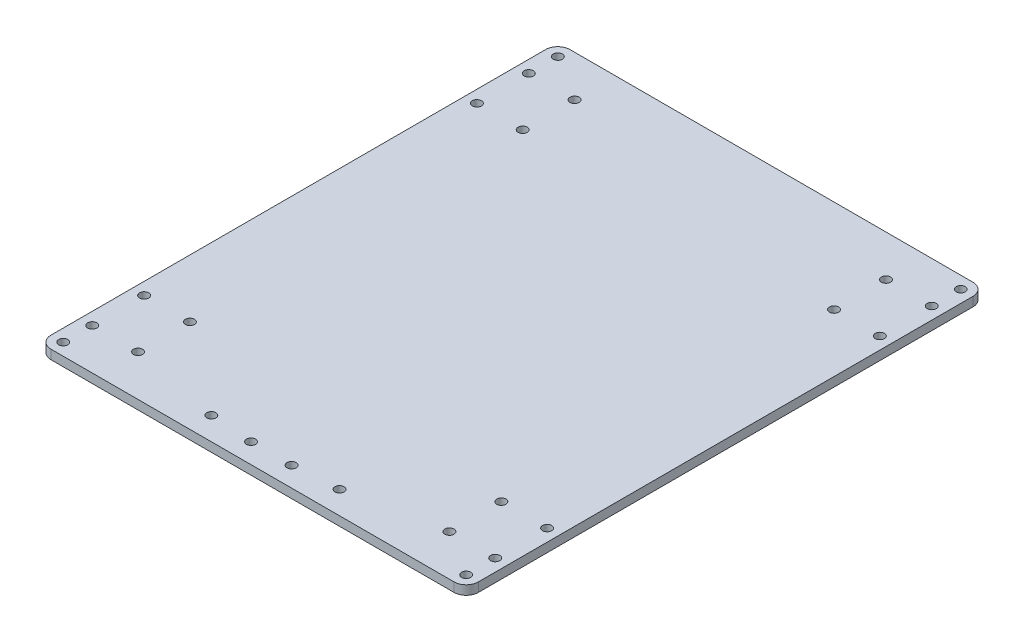
SolidWorks part; units mm, degrees
material "Beech"
ref_plane "Front Plane" through (0, 0, 0) normal (0, 0, 1) x (1, 0, 0)
ref_plane "Top Plane" through (0, 0, 0) normal (0, 1, 0) x (1, 0, 0)
ref_plane "Right Plane" through (0, 0, 0) normal (1, 0, 0) x (0, 0, -1)
sketch "Sketch1" plane through (0, 0, 0) normal (0, 1, 0) x (1, 0, 0)
  line L0 (-4, 0) -> (-136, 0)
  line L1 (-140, 4) -> (-140, 166)
  line L2 (-136, 170) -> (-4, 170)
  line L3 (0, 166) -> (0, 4)
  arc A0 (-136, 0) -> (-140, 4) centre (-136, 4) cw
  arc A1 (-4, 0) -> (0, 4) centre (-4, 4) ccw
  arc A2 (-4, 170) -> (0, 166) centre (-4, 166) cw
  arc A3 (-140, 166) -> (-136, 170) centre (-136, 166) cw
  circle A4 centre (-136, 166) radius 1.5
  circle A5 centre (-4, 166) radius 1.5
  circle A6 centre (-136, 4) radius 1.5
  circle A7 centre (-4, 4) radius 1.5
  circle A8 centre (-121, 156.5) radius 1.5
  circle A9 centre (-136, 156.5) radius 1.5
  circle A10 centre (-136, 139.5) radius 1.5
  circle A11 centre (-121, 139.5) radius 1.5
  circle A12 centre (-19, 156.5) radius 1.5
  circle A13 centre (-4, 156.5) radius 1.5
  circle A14 centre (-4, 139.5) radius 1.5
  circle A15 centre (-19, 139.5) radius 1.5
  circle A16 centre (-63.6907, 6.5) radius 1.5
  circle A17 centre (-77, 6.5) radius 1.5
  circle A19 centre (-121, 30.5) radius 1.5
  circle A20 centre (-136, 30.5) radius 1.5
  circle A21 centre (-136, 13.5) radius 1.5
  circle A22 centre (-121, 13.5) radius 1.5
  circle A23 centre (-19, 30.5) radius 1.5
  circle A24 centre (-4, 30.5) radius 1.5
  circle A25 centre (-19, 13.5) radius 1.5
  circle A26 centre (-4, 13.5) radius 1.5
  circle A31 centre (-91, 7.5) radius 1.5
  circle A33 centre (-49, 7.5) radius 1.5
  point P7 (-140, 0)
  point P10 (0, 0)
  point P13 (0, 170)
  point P16 (-140, 170)
  dimension "D3" = 4
  dimension "D1" = 140
  dimension "D2" = 170
extrude "Boss-Extrude1" add sketch "Sketch1" along normal blind 3
